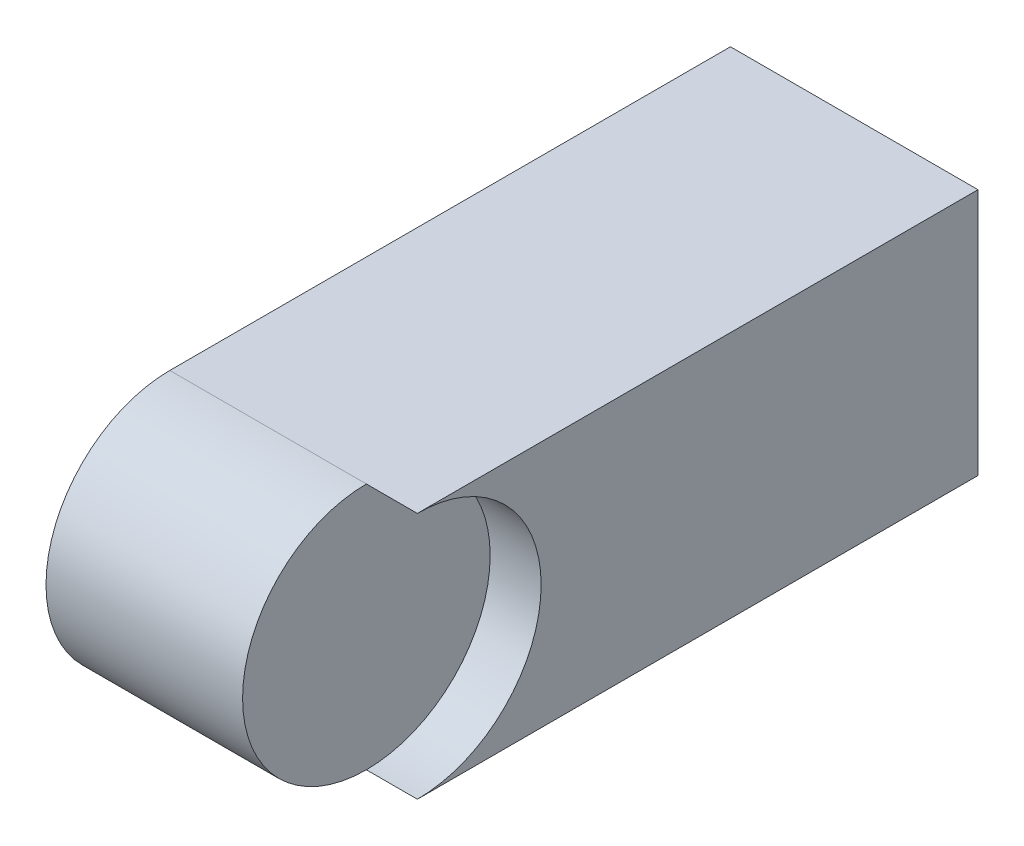
SolidWorks part; units mm, degrees
ref_plane "Front Plane" through (0, 0, 0) normal (0, 0, 1) x (1, 0, 0)
ref_plane "Top Plane" through (0, 0, 0) normal (0, 1, 0) x (1, 0, 0)
ref_plane "Right Plane" through (0, 0, 0) normal (1, 0, 0) x (0, 0, -1)
sketch "Sketch2" plane through (0, 0, 0) normal (0, 0, 1) x (1, 0, 0)
  line L1 (-8.5, -8.5) -> (8.5, -8.5)
  line L2 (-8.5, -8.5) -> (-8.5, 8.5)
  line L3 (-8.5, 8.5) -> (8.5, 8.5)
  line L4 (8.5, -8.5) -> (8.5, 8.5)
  line L5 (-8.5, -8.5) -> (8.5, 8.5) construction
  line L6 (-8.5, 8.5) -> (8.5, -8.5) construction
  point P0 (0, 0)
  dimension "D1" = 17
  dimension "D2" = 17
extrude "Boss-Extrude1" add sketch "Sketch2" along normal blind 47
sketch "Sketch3" plane through (8.5, 0, 0) normal (1, 0, 0) x (0, 0, -1)
  line L0 (0, 0) -> (-47, -8.5) construction
  line L1 (0, -8.5) -> (0, 8.5) construction
  line L2 (-47, -8.5) -> (-39.5, -8.5) construction
  line L3 (-47, -8.5) -> (0, -8.5) construction
  line L4 (-47, 0) -> (-38.5, 0) construction
  line L5 (-47, 8.5) -> (0, 8.5) construction
  line L6 (-39.5, 8.5) -> (-47, 8.5)
  line L10 (-47, -8.5) -> (-47, 8.5) construction
  line L11 (-38.5, -8.5) -> (-47, -8.5)
  line L12 (-47, -8.5) -> (-47, 0)
  line L13 (-47, 0) -> (-47, 8.5)
  line L14 (-47, 8.5) -> (-38.5, 8.5)
  arc A1 (-38.5, 8.5) -> (-38.5, -8.5) centre (-38.5, 0) ccw
  dimension "D1" = 8.5
extrude "Cut-Extrude1" cut sketch "Sketch3" against normal blind 47
sketch "Sketch6" plane through (8.5, 0, 0) normal (1, 0, 0) x (0, 0, -1)
  line L0 (-38.5, -8.5) -> (-38.5, 0) construction
  circle A0 centre (-38.5, 0) radius 8.5
extrude "Cut-Extrude3" cut sketch "Sketch6" against normal blind 3.5
